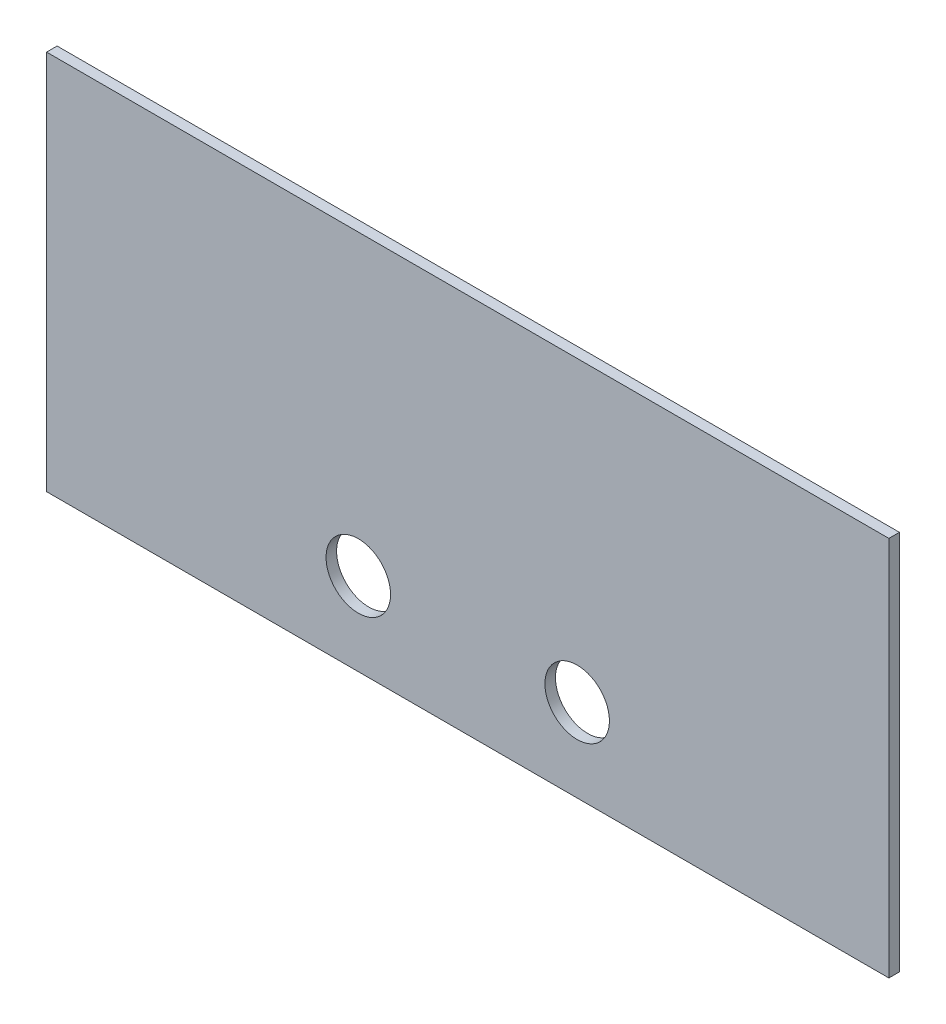
SolidWorks part; units mm, degrees
material "Acrylic (Medium-high impact)"
ref_plane "Front Plane" through (0, 0, 0) normal (0, 0, 1) x (1, 0, 0)
ref_plane "Top Plane" through (0, 0, 0) normal (0, 1, 0) x (1, 0, 0)
ref_plane "Right Plane" through (0, 0, 0) normal (1, 0, 0) x (0, 0, -1)
sketch "Sketch1" plane through (0, 0, 0) normal (0, 0, 1) x (1, 0, 0)
  line L2 (0, 0) -> (127, 0)
  line L3 (0, 0) -> (0, 57.404)
  line L4 (0, 57.404) -> (127, 57.404)
  line L7 (127, 0) -> (127, 57.404)
  circle A0 centre (80, 12.5001) radius 4.864 construction
  circle A1 centre (47, 12.5001) radius 4.864 construction
  circle A2 centre (80, 12.5001) radius 4.864
  circle A3 centre (47, 12.5001) radius 4.864
  dimension "D1" = 57.404
  dimension "D2" = 127
extrude "Boss-Extrude1" add sketch "Sketch1" along normal blind 1.5875
